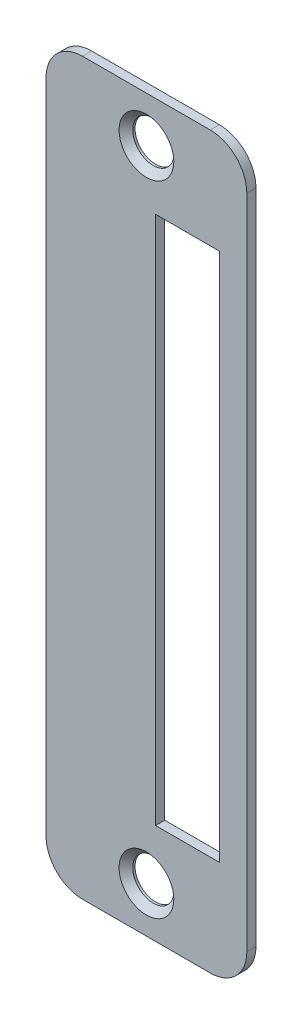
SolidWorks part; units mm, degrees
ref_plane "Planta" through (0, 0, 0) normal (0, 0, 1) x (1, 0, 0)
ref_plane "Alzado" through (0, 0, 0) normal (0, 1, 0) x (1, 0, 0)
ref_plane "Vista lateral" through (0, 0, 0) normal (1, 0, 0) x (0, 0, -1)
sketch "Croquis1" plane through (0, 0, 0) normal (0, 0, 1) x (1, 0, 0)
  line L2 (8, -29) -> (8, 29)
  line L4 (-11, 36) -> (-11, -36)
  line L5 (-7, -40) -> (7, -40)
  line L6 (11, -36) -> (11, 36)
  line L7 (7, 40) -> (-7, 40)
  line L8 (1, 29) -> (1, -29)
  line L9 (8, 29) -> (1, 29)
  line L10 (8, -29) -> (1, -29)
  arc A0 (-7, -40) -> (-11, -36) centre (-7, -36) cw
  arc A1 (11, -36) -> (7, -40) centre (7, -36) cw
  arc A2 (-7, 40) -> (-11, 36) centre (-7, 36) ccw
  arc A3 (11, 36) -> (7, 40) centre (7, 36) ccw
  circle A4 centre (0, 35) radius 2
  circle A5 centre (0, -35) radius 2
  point P3 (-11, -40)
  point P9 (11, -40)
  point P13 (-11, 40)
  dimension "D3" = 4
  dimension "D4" = 4
  dimension "D9" = 4
  dimension "D1" = 22
  dimension "D2" = 80
  dimension "D5" = 58
  dimension "D6" = 7
  dimension "D7" = 11
  dimension "D8" = 3
extrude "Saliente-Extruir1" add sketch "Croquis1" along normal blind 1
hole_wizard "Avellanado para tornillo con cabeza elevada avellanada de M41" positions "Croquis7" profile "Croquis6" countersink size "M4" standard "ISO" end condition up to next
sketch "Croquis7" plane through (0, 0, 1) normal (0, 0, 1) x (1, 0, 0)
  point P0 (0, 35)
  point P4 (0, -35)
sketch "Croquis6" plane through (0, 35, 1) normal (1, 0, 0) x (0, -1, 0)
  line L0 (0, 0) -> (0, 1)
  line L1 (0, 1) -> (2.25, 1)
  line L2 (2.25, 1) -> (2.25, 0.75)
  line L3 (2.25, 0.75) -> (3, 0)
  line L5 (3, 0) -> (0, 0)
  line L6 (-2.25, 0.75) -> (-3, 0) construction
  line L11 (0, -6.35) -> (0, 107.95) construction
  dimension "Diámetro de taladro hasta el siguiente" = 4.5
  dimension "Profundidad de taladro hasta el siguiente" = 1
  dimension "Diámetro de avellanado cercano" = 6
  dimension "Ángulo de avellanado cercano" = 90
